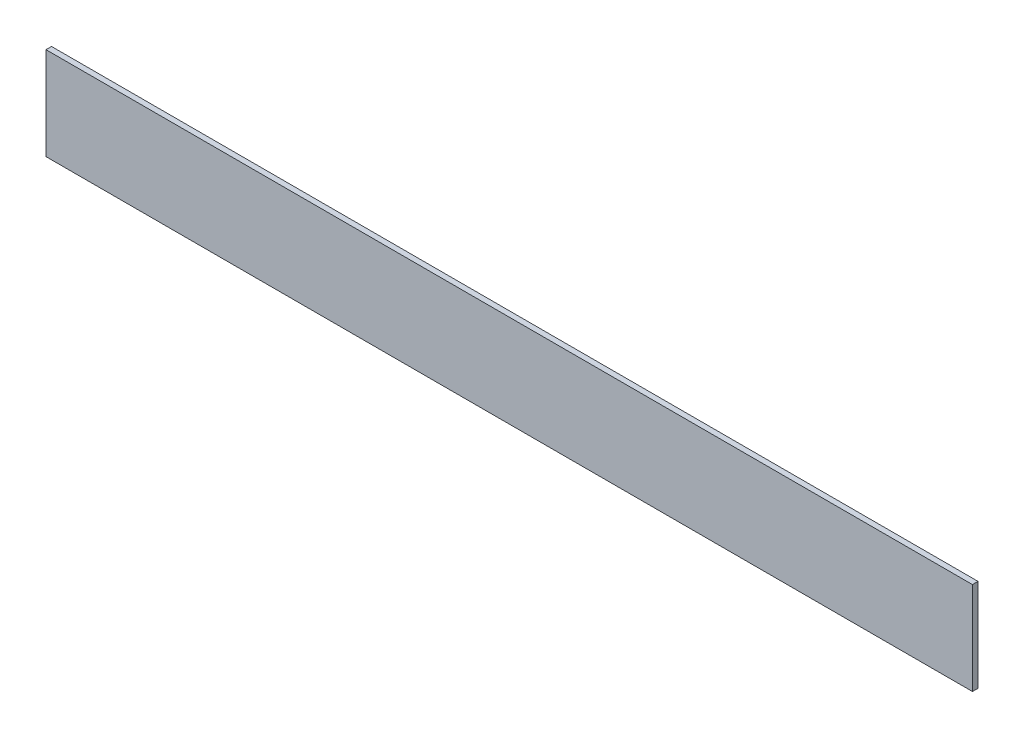
SolidWorks part; units mm, degrees
ref_plane "Plan de face" through (0, 0, 0) normal (0, 0, 1) x (1, 0, 0)
ref_plane "Plan de dessus" through (0, 0, 0) normal (0, 1, 0) x (1, 0, 0)
ref_plane "Plan de droite" through (0, 0, 0) normal (1, 0, 0) x (0, 0, -1)
sketch "Esquisse1" plane through (0, 0, 0) normal (0, 0, 1) x (1, 0, 0)
  line L0 (760.8421, 19.4529) -> (260.8421, 19.4529)
  line L3 (260.8421, 19.4529) -> (260.8421, -30.5471)
  line L6 (260.8421, -30.5471) -> (760.8421, -30.5471)
  line L7 (760.8421, 19.4529) -> (760.8421, -30.5471)
  dimension "D3" = 500
  dimension "D4" = 50
extrude "Boss.-Extru.1" add sketch "Esquisse1" along normal blind 3
sketch "Esquisse2" plane through (0, 0, 3) normal (0, 0, 1) x (1, 0, 0)
